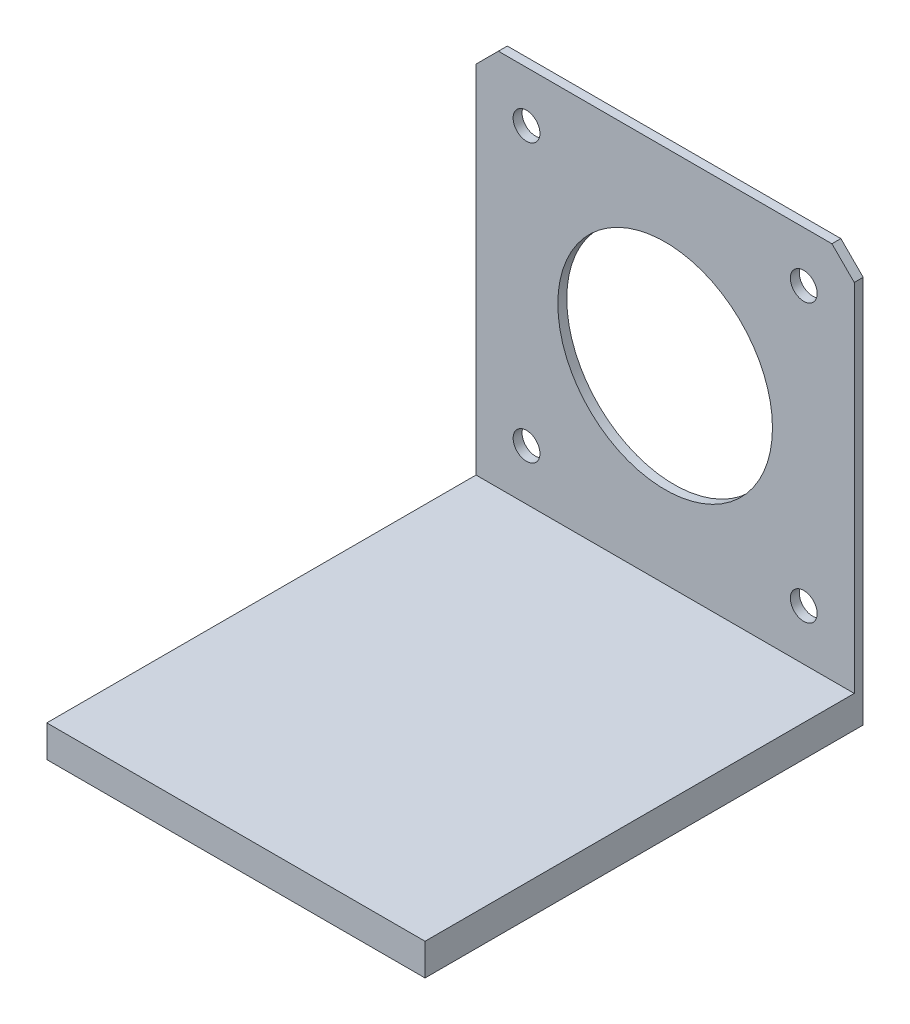
SolidWorks part; units mm, degrees
ref_plane "Alzado" through (0, 0, 0) normal (0, 0, 1) x (1, 0, 0)
ref_plane "Planta" through (0, 0, 0) normal (0, 1, 0) x (1, 0, 0)
ref_plane "Vista lateral" through (0, 0, 0) normal (1, 0, 0) x (0, 0, -1)
sketch "Sketch1" plane through (0, 0, 0) normal (0, 0, 1) x (1, 0, 0)
  line L1 (-25.8145, 17.8273) -> (16.4855, 17.8273)
  line L2 (-25.8145, 17.8273) -> (-25.8145, -24.4727)
  line L3 (-25.8145, -24.4727) -> (16.4855, -24.4727)
  line L4 (16.4855, 17.8273) -> (16.4855, -24.4727)
  dimension "D1" = 42.3
  dimension "D2" = 42.3
extrude "Boss-Extrude1" add sketch "Sketch1" along normal blind 1
sketch "Sketch3" plane through (0, 0, 1) normal (0, 0, 1) x (1, 0, 0)
  line L0 (-25.8145, -24.4727) -> (16.4855, -24.4727) construction
  line L1 (-25.8145, 17.8273) -> (-25.8145, -24.4727) construction
  circle A0 centre (-20.1645, -18.8227) radius 0.5
  circle A1 centre (10.8355, -18.8227) radius 0.5
  circle A2 centre (10.8355, 12.1773) radius 0.5
  circle A3 centre (-20.1645, 12.1773) radius 0.5
  dimension "D1" = 5.65
  dimension "D3" = 31
  dimension "D4" = 31
  dimension "D5" = 31
  dimension "D2" = 5.65
extrude "Cut-Extrude1" cut sketch "Sketch3" against normal through all
chamfer "Chamfer1" distance 2.5 angle 45 4 edges at (-25.8145, -24.4727, 0.5) (16.4855, -24.4727, 0.5) (16.4855, 17.8273, 0.5) (-25.8145, 17.8273, 0.5)
sketch "Sketch4" plane through (0, 0, 1) normal (0, 0, 1) x (1, 0, 0)
  circle A0 centre (-4.6645, -3.3227) radius 12
extrude "Cut-Extrude2" cut sketch "Sketch4" against normal through all
sketch "Sketch5" plane through (0, 0, 1) normal (0, 0, 1) x (1, 0, 0)
  circle A0 centre (-20.1645, 12.1773) radius 1.5
  circle A1 centre (-20.1645, -18.8227) radius 1.5
  circle A2 centre (10.8355, -18.8227) radius 1.5
  circle A3 centre (10.8355, 12.1773) radius 1.5
extrude "Cut-Extrude3" cut sketch "Sketch5" against normal through all
sketch "Sketch6" plane through (0, -24.4727, 0) normal (0, -1, 0) x (1, 0, 0)
  line L1 (-25.8145, 1) -> (16.4855, 1)
  line L2 (-25.8145, 1) -> (-25.8145, 0)
  line L3 (-25.8145, 0) -> (16.4855, 0)
  line L4 (16.4855, 1) -> (16.4855, 0)
extrude "Boss-Extrude2" add sketch "Sketch6" along normal blind 3.21
sketch "Sketch7" plane through (0, 0, 1) normal (0, 0, 1) x (1, 0, 0)
  line L1 (-25.8145, -21.9727) -> (16.4855, -21.9727)
  line L2 (-25.8145, -21.9727) -> (-25.8145, -27.6827)
  line L3 (-25.8145, -27.6827) -> (16.4855, -27.6827)
  line L4 (16.4855, -21.9727) -> (16.4855, -27.6827)
extrude "Boss-Extrude3" add sketch "Sketch7" against normal blind 1
sketch "Sketch8" plane through (0, -27.6827, 0) normal (0, -1, 0) x (1, 0, 0)
  line L1 (-25.8145, 1) -> (16.4855, 1)
  line L2 (-25.8145, 1) -> (-25.8145, 0)
  line L3 (-25.8145, 0) -> (16.4855, 0)
  line L4 (16.4855, 1) -> (16.4855, 0)
extrude "Boss-Extrude4" add sketch "Sketch8" along normal blind 0.35
sketch "Sketch9" plane through (0, 0, 1) normal (0, 0, 1) x (1, 0, 0)
  line L5 (-25.8145, -28.0327) -> (-25.8145, -25.4727) construction
  line L6 (-25.8145, 15.3273) -> (-25.8145, -28.0327) construction
  line L7 (16.4855, -28.0327) -> (16.4855, 15.3273) construction
  line L8 (-25.8145, -25.4727) -> (16.4855, -25.4727)
  line L9 (-25.8145, -25.4727) -> (-25.8145, -24.4727)
  line L10 (-25.8145, -24.4727) -> (16.4855, -24.4727)
  line L11 (16.4855, -25.4727) -> (16.4855, -24.4727)
  dimension "D1" = 2.56
  dimension "D2" = 1
extrude "Boss-Extrude5" add sketch "Sketch9" along normal blind 48
sketch "Sketch10" plane through (0, -25.4727, 0) normal (0, -1, 0) x (1, 0, 0)
  line L0 (16.4855, 49) -> (16.4855, 1) construction
  line L1 (-25.8145, 49) -> (16.4855, 49)
  line L2 (-25.8145, 49) -> (-25.8145, 48)
  line L3 (-25.8145, 48) -> (16.4855, 48)
  line L4 (16.4855, 49) -> (16.4855, 48)
  dimension "D1" = 1
extrude "Boss-Extrude6" add sketch "Sketch10" along normal blind 2.56
sketch "Sketch11" plane through (-25.8145, 0, 0) normal (-1, 0, 0) x (0, 0, 1)
  line L1 (0, -28.0327) -> (49, -28.0327)
  line L2 (0, -28.0327) -> (0, -24.4727)
  line L3 (0, -24.4727) -> (49, -24.4727)
  line L4 (49, -28.0327) -> (49, -24.4727)
extrude "Boss-Extrude7" add sketch "Sketch11" against normal blind 1
sketch "Sketch12" plane through (-25.8145, 0, 0) normal (-1, 0, 0) x (0, 0, 1)
  line L0 (49, -28.0327) -> (0, -28.0327) construction
  line L1 (22, -28.0327) -> (27, -28.0327)
  line L2 (22, -28.0327) -> (22, -27.0327)
  line L3 (22, -27.0327) -> (27, -27.0327)
  line L4 (27, -28.0327) -> (27, -27.0327)
  dimension "D1" = 1
  dimension "D2" = 5
  dimension "D3" = 22
extrude "Boss-Extrude8" add sketch "Sketch12" along normal blind 5
sketch "Sketch13" plane through (16.4855, 0, 0) normal (1, 0, 0) x (0, 0, -1)
  line L1 (-49, -24.4727) -> (0, -24.4727)
  line L2 (-49, -24.4727) -> (-49, -28.0327)
  line L3 (-49, -28.0327) -> (0, -28.0327)
  line L4 (0, -24.4727) -> (0, -28.0327)
extrude "Boss-Extrude9" add sketch "Sketch13" against normal blind 1
sketch "Sketch14" plane through (0, -24.4727, 0) normal (0, 1, 0) x (1, 0, 0)
  line L0 (-25.8145, -27) -> (16.4855, -27) construction
  line L1 (16.4855, -49) -> (16.4855, -1) construction
  line L3 (16.4855, -27) -> (21.4855, -27)
  line L4 (16.4855, -27) -> (16.4855, -22)
  line L5 (16.4855, -22) -> (21.4855, -22)
  line L6 (21.4855, -27) -> (21.4855, -22)
  dimension "D1" = 5
  dimension "D2" = 5
extrude "Boss-Extrude10" add sketch "Sketch14" against normal up to vertex (3.56 mm away)
sketch "Sketch15" plane through (21.4855, 0, 0) normal (1, 0, 0) x (0, 0, -1)
  line L0 (-27, -28.0327) -> (-27, -24.4727) construction
  line L1 (-22, -24.4727) -> (-27, -24.4727)
  line L2 (-22, -24.4727) -> (-22, -27.0327)
  line L3 (-22, -27.0327) -> (-27, -27.0327)
  line L4 (-27, -24.4727) -> (-27, -27.0327)
  dimension "D1" = 1
extrude "Cut-Extrude4" cut sketch "Sketch15" against normal blind 5
sketch "Sketch16" plane through (0, -27.0327, 0) normal (0, 1, 0) x (1, 0, 0)
  circle A0 centre (-28.3145, -24.5) radius 1
  circle A1 centre (18.9855, -24.5) radius 1
extrude "Cut-Extrude5" cut sketch "Sketch16" against normal blind 5
sketch "Sketch17" plane through (0, -27.0327, 0) normal (0, 1, 0) x (1, 0, 0)
  line L1 (-30.8145, -27) -> (-25.8145, -27)
  line L2 (-30.8145, -27) -> (-30.8145, -22)
  line L3 (-30.8145, -22) -> (-25.8145, -22)
  line L4 (-25.8145, -27) -> (-25.8145, -22)
  circle A0 centre (-28.3145, -24.5) radius 1
extrude "Boss-Extrude11" add sketch "Sketch17" along normal up to vertex
sketch "Sketch19" plane through (0, -24.4727, 0) normal (0, 1, 0) x (1, 0, 0)
  line L1 (-29.4692, -26.5) -> (-27.1598, -26.5)
  line L2 (-27.1598, -26.5) -> (-26.0051, -24.5)
  line L3 (-26.0051, -24.5) -> (-27.1598, -22.5)
  line L4 (-27.1598, -22.5) -> (-29.4692, -22.5)
  line L5 (-29.4692, -22.5) -> (-30.6239, -24.5)
  line L6 (-30.6239, -24.5) -> (-29.4692, -26.5)
  circle A0 centre (-28.3145, -24.5) radius 2 construction
extrude "Cut-Extrude6" cut sketch "Sketch19" against normal blind 5
sketch "Sketch20" plane through (-30.8145, 0, 0) normal (-1, 0, 0) x (0, 0, 1)
  line L1 (27, -24.4727) -> (22, -24.4727)
  line L2 (27, -24.4727) -> (27, -28.0327)
  line L3 (27, -28.0327) -> (22, -28.0327)
  line L4 (22, -24.4727) -> (22, -28.0327)
extrude "Boss-Extrude12" add sketch "Sketch20" along normal blind 1
sketch "Sketch21" plane through (0, 0, 27) normal (0, 0, 1) x (1, 0, 0)
  line L1 (-25.8145, -24.4727) -> (-31.8145, -24.4727)
  line L2 (-25.8145, -24.4727) -> (-25.8145, -28.0327)
  line L3 (-25.8145, -28.0327) -> (-31.8145, -28.0327)
  line L4 (-31.8145, -24.4727) -> (-31.8145, -28.0327)
extrude "Boss-Extrude13" add sketch "Sketch21" along normal blind 1
sketch "Sketch22" plane through (0, 0, 22) normal (0, 0, -1) x (-1, 0, 0)
  line L1 (31.8145, -24.4727) -> (25.8145, -24.4727)
  line L2 (31.8145, -24.4727) -> (31.8145, -28.0327)
  line L3 (31.8145, -28.0327) -> (25.8145, -28.0327)
  line L4 (25.8145, -24.4727) -> (25.8145, -28.0327)
extrude "Boss-Extrude14" add sketch "Sketch22" along normal blind 1
sketch "Sketch23" plane through (0, -27.0327, 0) normal (0, 1, 0) x (1, 0, 0)
  line L1 (21.4855, -27) -> (16.4855, -27)
  line L2 (21.4855, -27) -> (21.4855, -22)
  line L3 (21.4855, -22) -> (16.4855, -22)
  line L4 (16.4855, -27) -> (16.4855, -22)
extrude "Boss-Extrude15" add sketch "Sketch23" along normal up to vertex
sketch "Sketch24" plane through (0, 0, 27) normal (0, 0, 1) x (1, 0, 0)
  line L1 (21.4855, -24.4727) -> (16.4855, -24.4727)
  line L2 (21.4855, -24.4727) -> (21.4855, -28.0327)
  line L3 (21.4855, -28.0327) -> (16.4855, -28.0327)
  line L4 (16.4855, -24.4727) -> (16.4855, -28.0327)
extrude "Boss-Extrude16" add sketch "Sketch24" along normal blind 1
sketch "Sketch25" plane through (0, 0, 22) normal (0, 0, -1) x (-1, 0, 0)
  line L1 (-21.4855, -24.4727) -> (-16.4855, -24.4727)
  line L2 (-21.4855, -24.4727) -> (-21.4855, -28.0327)
  line L3 (-21.4855, -28.0327) -> (-16.4855, -28.0327)
  line L4 (-16.4855, -24.4727) -> (-16.4855, -28.0327)
extrude "Boss-Extrude17" add sketch "Sketch25" along normal blind 1
sketch "Sketch26" plane through (21.4855, 0, 0) normal (1, 0, 0) x (0, 0, -1)
  line L1 (-28, -24.4727) -> (-21, -24.4727)
  line L2 (-28, -24.4727) -> (-28, -28.0327)
  line L3 (-28, -28.0327) -> (-21, -28.0327)
  line L4 (-21, -24.4727) -> (-21, -28.0327)
extrude "Boss-Extrude18" add sketch "Sketch26" along normal blind 1
sketch "Sketch29" plane through (0, -24.4727, 0) normal (0, 1, 0) x (1, 0, 0)
  line L0 (22.4855, -24.5) -> (19.4855, -24.5) construction
  line L1 (22.4855, -21) -> (22.4855, -28) construction
  line L3 (20.6402, -26.5) -> (21.7949, -24.5)
  line L4 (21.7949, -24.5) -> (20.6402, -22.5)
  line L5 (20.6402, -22.5) -> (18.3308, -22.5)
  line L6 (18.3308, -22.5) -> (17.1761, -24.5)
  line L7 (17.1761, -24.5) -> (18.3308, -26.5)
  line L8 (18.3308, -26.5) -> (20.6402, -26.5)
  circle A0 centre (19.4855, -24.5) radius 2 construction
extrude "Cut-Extrude7" cut sketch "Sketch29" against normal blind 21
sketch "Sketch31" plane through (0, -24.4727, 0) normal (0, 1, 0) x (1, 0, 0)
  line L1 (22.4855, -21) -> (16.4855, -21)
  line L2 (22.4855, -21) -> (22.4855, -28)
  line L3 (22.4855, -28) -> (16.4855, -28)
  line L4 (16.4855, -21) -> (16.4855, -28)
extrude "Cut-Extrude8" cut sketch "Sketch31" against normal through all
sketch "Sketch32" plane through (0, -25.4727, 0) normal (0, -1, 0) x (1, 0, 0)
  line L0 (-24.8145, 1) -> (-24.8145, 48) construction
  line L1 (-24.8145, 28) -> (-18.8145, 28)
  line L2 (-24.8145, 28) -> (-24.8145, 21)
  line L3 (-24.8145, 21) -> (-18.8145, 21)
  line L4 (-18.8145, 28) -> (-18.8145, 21)
  dimension "D1" = 6
extrude "Boss-Extrude19" add sketch "Sketch32" along normal up to vertex (2.56 mm away)
sketch "Sketch34" plane through (0, -28.0327, 0) normal (0, -1, 0) x (-1, 0, 0)
  line L0 (18.8145, -28) -> (-15.4855, -28) construction
  line L1 (-15.4855, -48) -> (-15.4855, -1) construction
  line L3 (-15.4855, -28) -> (-9.4855, -28)
  line L4 (-15.4855, -28) -> (-15.4855, -21)
  line L5 (-15.4855, -21) -> (-9.4855, -21)
  line L6 (-9.4855, -28) -> (-9.4855, -21)
  dimension "D1" = 6
extrude "Boss-Extrude20" add sketch "Sketch34" against normal up to vertex
sketch "Sketch35" plane through (0, -28.0327, 0) normal (0, -1, 0) x (1, 0, 0)
  line L1 (-25.8145, 28) -> (-31.8145, 28)
  line L2 (-25.8145, 28) -> (-25.8145, 21)
  line L3 (-25.8145, 21) -> (-31.8145, 21)
  line L4 (-31.8145, 28) -> (-31.8145, 21)
extrude "Cut-Extrude9" cut sketch "Sketch35" against normal through all
